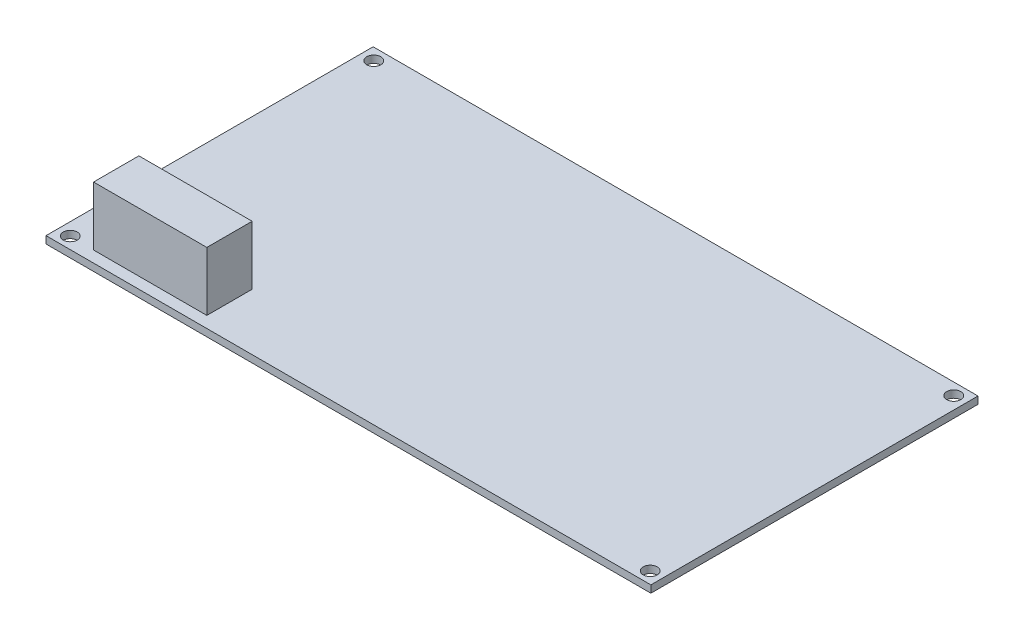
SolidWorks part; units mm, degrees
ref_plane "Front Plane" through (0, 0, 0) normal (0, 0, 1) x (1, 0, 0)
ref_plane "Top Plane" through (0, 0, 0) normal (0, 1, 0) x (1, 0, 0)
ref_plane "Right Plane" through (0, 0, 0) normal (1, 0, 0) x (0, 0, -1)
sketch "Sketch1" plane through (0, 0, 0) normal (0, 1, 0) x (1, 0, 0)
  line L0 (66.75, 72.2) -> (66.75, 69.6) construction
  line L1 (0, 0) -> (133.5, 0)
  line L2 (0, 0) -> (0, 72.2)
  line L3 (0, 72.2) -> (133.5, 72.2)
  line L4 (133.5, 0) -> (133.5, 72.2)
  line L5 (2.75, 69.6) -> (130.75, 69.6) construction
  line L6 (2.75, 69.6) -> (2.75, 2.6) construction
  line L7 (2.75, 2.6) -> (130.75, 2.6) construction
  line L8 (130.75, 69.6) -> (130.75, 2.6) construction
  line L9 (0, 36.1) -> (2.75, 36.1)
  circle A0 centre (2.75, 69.6) radius 1.55
  circle A1 centre (130.75, 69.6) radius 1.55
  circle A2 centre (130.75, 2.6) radius 1.55
  circle A3 centre (2.75, 2.6) radius 1.55
  dimension "D3" = 3.1
  dimension "D1" = 133.5
  dimension "D2" = 72.2
  dimension "D4" = 128
  dimension "D5" = 67
extrude "Boss-Extrude1" add sketch "Sketch1" along normal blind 1.6
sketch "Sketch2" plane through (0, 1.6, 0) normal (0, 1, 0) x (1, 0, 0)
  line L1 (8, 2.5) -> (33, 2.5)
  line L2 (8, 2.5) -> (8, 12.5)
  line L3 (8, 12.5) -> (33, 12.5)
  line L4 (33, 2.5) -> (33, 12.5)
  line L7 (0, 0) -> (133.5, 0) construction
  line L8 (0, 0) -> (0, 72.2) construction
  dimension "D1" = 10
  dimension "D2" = 25
  dimension "D3" = 2.5
  dimension "D4" = 8
extrude "Boss-Extrude2" add sketch "Sketch2" along normal blind 13
ref_plane "Plane1" through (0, 0, -36.1) normal (0, 0, 1) x (1, 0, 0)
